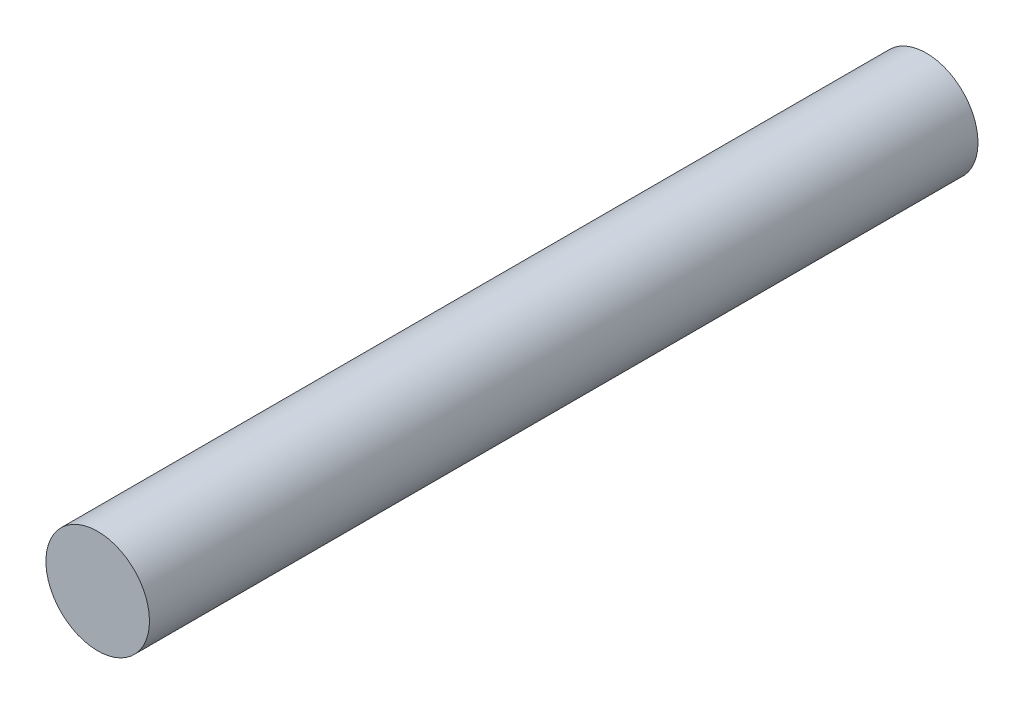
SolidWorks part; units mm, degrees
ref_plane "Спереди" through (0, 0, 0) normal (0, 0, 1) x (1, 0, 0)
ref_plane "Сверху" through (0, 0, 0) normal (0, 1, 0) x (1, 0, 0)
ref_plane "Справа" through (0, 0, 0) normal (1, 0, 0) x (0, 0, -1)
sketch "Эскиз1" plane through (0, 0, 0) normal (0, 0, 1) x (1, 0, 0)
  circle A0 centre (0, 0) radius 2.5
  dimension "D1" = 5
extrude "Бобышка-Вытянуть1" add sketch "Эскиз1" along normal blind 40
